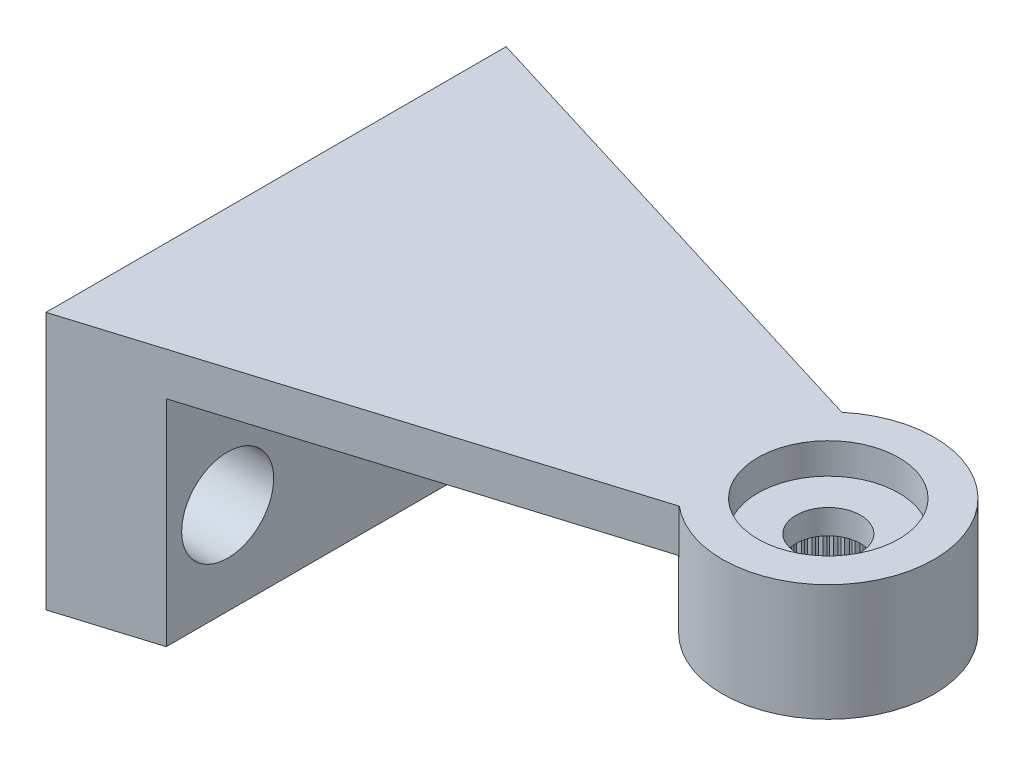
SolidWorks part; units mm, degrees
material "PVC Rígido"
ref_plane "Plano frontal" through (0, 0, 0) normal (0, 0, 1) x (1, 0, 0)
ref_plane "Plano superior" through (0, 0, 0) normal (0, 1, 0) x (1, 0, 0)
ref_plane "Plano direito" through (0, 0, 0) normal (1, 0, 0) x (0, 0, -1)
sketch "Esboço1" plane through (0, 0, 0) normal (0, 1, 0) x (1, 0, 0)
  line L0 (0, 0) -> (-18, 0) construction
  line L1 (-18, 7.5) -> (-2.2091, 2.65)
  line L2 (-2.2091, -2.65) -> (-18, -7.5)
  line L3 (-18, 7.5) -> (-18, -7.5)
  arc A0 (-2.2091, -2.65) -> (-2.2091, 2.65) centre (0, 0) ccw
  point P5 (0, 0)
  dimension "D1" = 6.9
  dimension "D2" = 18
  dimension "D3" = 15
  dimension "D4" = 5.3
extrude "Ressalto-extrusão1" add sketch "Esboço1" against normal blind 1.4
sketch "Esboço2" plane through (0, -1.4, 0) normal (0, -1, 0) x (1, 0, 0)
  arc A0 (-2.2091, -2.65) -> (-2.2091, 2.65) centre (0, 0) ccw construction
  circle A1 centre (0, 0) radius 3.45
extrude "Ressalto-extrusão2" add sketch "Esboço2" along normal offset from surface (2.4 mm away) 3.8 up to face at (-8.6898, 0, 0)
hole_wizard "Furo1" positions "Esboço3" profile "Esboço4" legacy
sketch "Esboço3" plane through (0, -3.8, 0) normal (0, -1, 0) x (-1, 0, 0)
  point P0 (0, 0)
sketch "Esboço4" plane through (0, -3.8, 0) normal (1, 0, 0) x (0, 0, -1)
  line L0 (0, 0) -> (0, 2)
  line L1 (0, 2) -> (2.475, 2)
  line L2 (2.475, 2) -> (2.475, 0)
  line L3 (2.475, 0) -> (0, 0)
  line L4 (0, 110) -> (0, -10) construction
  dimension "Diameter" = 4.95
  dimension "Depth" = 2
hole_wizard "Furo2" positions "Esboço5" profile "Esboço6" legacy
sketch "Esboço5" plane through (0, 0, 0) normal (0, 1, 0) x (1, 0, 0)
  point P0 (0, 0)
sketch "Esboço6" plane through (0, 0, 0) normal (1, 0, 0) x (0, 0, 1)
  line L0 (0, 0) -> (0, 1)
  line L1 (0, 1) -> (2.3, 1)
  line L2 (2.3, 1) -> (2.3, 0)
  line L3 (2.3, 0) -> (0, 0)
  line L4 (0, 110) -> (0, -10) construction
  dimension "Diameter" = 4.6
  dimension "Depth" = 1
hole_wizard "Furo3" positions "Esboço7" profile "Esboço8" legacy end condition through all
sketch "Esboço7" plane through (0, 0, 0) normal (0, 1, 0) x (1, 0, 0)
  point P0 (0, 0)
sketch "Esboço8" plane through (0, 0, 0) normal (1, 0, 0) x (0, 0, 1)
  line L0 (0, 0) -> (0, 3.8)
  line L1 (0, 3.8) -> (1.05, 3.8)
  line L2 (1.05, 3.8) -> (1.05, 0)
  line L3 (1.05, 0) -> (0, 0)
  line L4 (0, 110) -> (0, -10) construction
  dimension "Diameter" = 2.1
  dimension "Depth" = 3.8
sketch "Esboço11" plane through (0, -3.8, 0) normal (0, -1, 0) x (1, 0, 0)
  line L0 (-0.0981, 2.4731) -> (0, 2.375)
  line L1 (0, 2.375) -> (0.0981, 2.4731)
  line L2 (0, 0) -> (0, 2.475) construction
  circle A0 centre (0, 0) radius 2.375 construction
  circle A1 centre (0, 0) radius 2.475
  arc A2 (0.0981, 2.4731) -> (-0.0981, 2.4731) centre (0, 0) ccw
  dimension "D3" = 4.75
  dimension "D2" = 0.1
  dimension "D1" = 0
extrude "Ressalto-extrusão3" add sketch "Esboço11" against normal up to surface (2 mm away) up to face at (0, -1.8, 1.05)
pattern_circular "PadrãoCircular1" count 60 over 360 about axis through (0, 0, 0) along (0, 1, 0) of "Ressalto-extrusão3"
sketch "Sketch1" plane through (0, -1.4, 0) normal (0, -1, 0) x (1, 0, 0)
  line L0 (-18, 7.5) -> (-15, 6.5786)
  line L1 (-18, 7.5) -> (-2.2091, 2.65) construction
  line L2 (-15, 6.5786) -> (-15, -6.5786)
  line L3 (-2.2091, -2.65) -> (-18, -7.5) construction
  line L4 (-15, -6.5786) -> (-18, -7.5)
  line L5 (-18, -7.5) -> (-18, 7.5)
  point P10 (-10.3888, -2.2051)
  dimension "D1" = 3
extrude "Boss-Extrude1" add sketch "Sketch1" along normal blind 7
sketch "Sketch2" plane through (-15, 0, 0) normal (1, 0, 0) x (0, 0, -1)
  line L1 (6.5786, -1.4) -> (-6.5786, -1.4) construction
  line L2 (6.5786, -8.4) -> (6.5786, -1.4) construction
  line L3 (0, 55) -> (0, -55) construction
  circle A0 centre (4.5786, -5.4) radius 1.5
  circle A1 centre (-4.5786, -5.4) radius 1.5
  point P2 (0, 0)
  point P8 (0, 0)
  dimension "D1" = 3
  dimension "D2" = 4
  dimension "D3" = 2
extrude "Cut-Extrude1" cut sketch "Sketch2" against normal up to next
